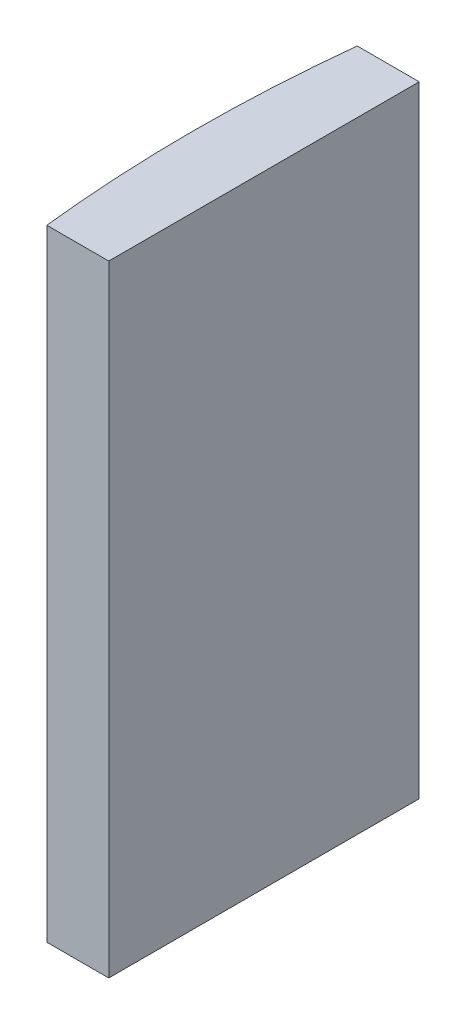
SolidWorks part; units mm, degrees
ref_plane "前视基准面" through (0, 0, 0) normal (0, 0, 1) x (1, 0, 0)
ref_plane "上视基准面" through (0, 0, 0) normal (0, 1, 0) x (1, 0, 0)
ref_plane "右视基准面" through (0, 0, 0) normal (1, 0, 0) x (0, 0, -1)
sketch "草图1" plane through (0, 0, 0) normal (0, 1, 0) x (1, 0, 0)
  line L0 (-137.6835, 0) -> (10.8051, 0) construction
  line L1 (-41.2214, 5) -> (-39.2248, 5)
  line L2 (-41.2214, -5) -> (-39.2248, -5)
  line L3 (-39.2248, 5) -> (-39.2248, -5)
  arc A0 (-41.2214, 5) -> (-41.2214, -5) centre (4.3552, 0) ccw
  point P2 (-41.4948, 0)
  point P4 (-39.2248, 0)
  dimension "D2" = 5
  dimension "D3" = 45.85
  dimension "D4" = 2.27
  dimension "D1" = 5
extrude "凸台-拉伸1" add sketch "草图1" along normal blind 20
